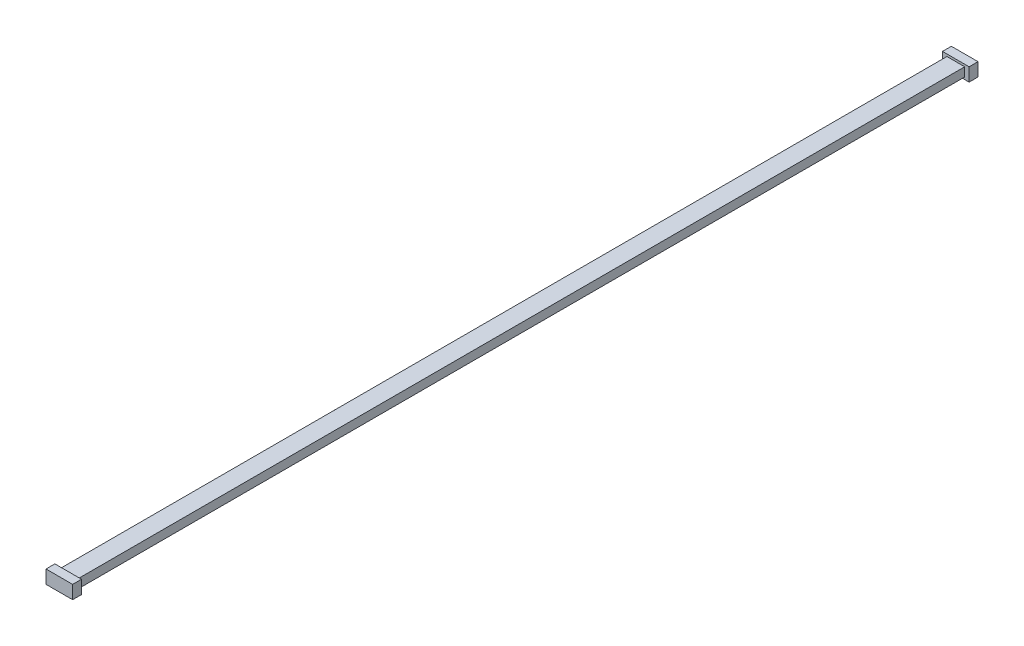
SolidWorks part; units mm, degrees
ref_plane "Plan de face" through (0, 0, 0) normal (0, 0, 1) x (1, 0, 0)
ref_plane "Plan de dessus" through (0, 0, 0) normal (0, 1, 0) x (1, 0, 0)
ref_plane "Plan de droite" through (0, 0, 0) normal (1, 0, 0) x (0, 0, -1)
sketch "Esquisse1" plane through (0, 0, 0) normal (0, 0, 1) x (1, 0, 0)
  line L1 (-10, 5) -> (10, 5)
  line L2 (-10, 5) -> (-10, -5)
  line L3 (-10, -5) -> (10, -5)
  line L4 (10, 5) -> (10, -5)
  line L5 (-10, 5) -> (10, -5) construction
  line L6 (-10, -5) -> (10, 5) construction
  point P0 (0, 0)
  dimension "D1" = 20
  dimension "D2" = 10
extrude "Boss.-Extru.1" add sketch "Esquisse1" along normal blind 500
sketch "Esquisse2" plane through (0, 0, 500) normal (0, 0, 1) x (1, 0, 0)
  line L1 (-15, 7.5) -> (15, 7.5)
  line L2 (-15, 7.5) -> (-15, -7.5)
  line L3 (-15, -7.5) -> (15, -7.5)
  line L4 (15, 7.5) -> (15, -7.5)
  line L5 (-15, 7.5) -> (15, -7.5) construction
  line L6 (-15, -7.5) -> (15, 7.5) construction
  point P0 (0, 0)
  dimension "D1" = 30
  dimension "D2" = 15
extrude "Boss.-Extru.2" add sketch "Esquisse2" along normal blind 10
mirror "Symétrie1" about plane through (0, 0, 0) normal (0, 0, 1) of "Boss.-Extru.2", "Boss.-Extru.1"
